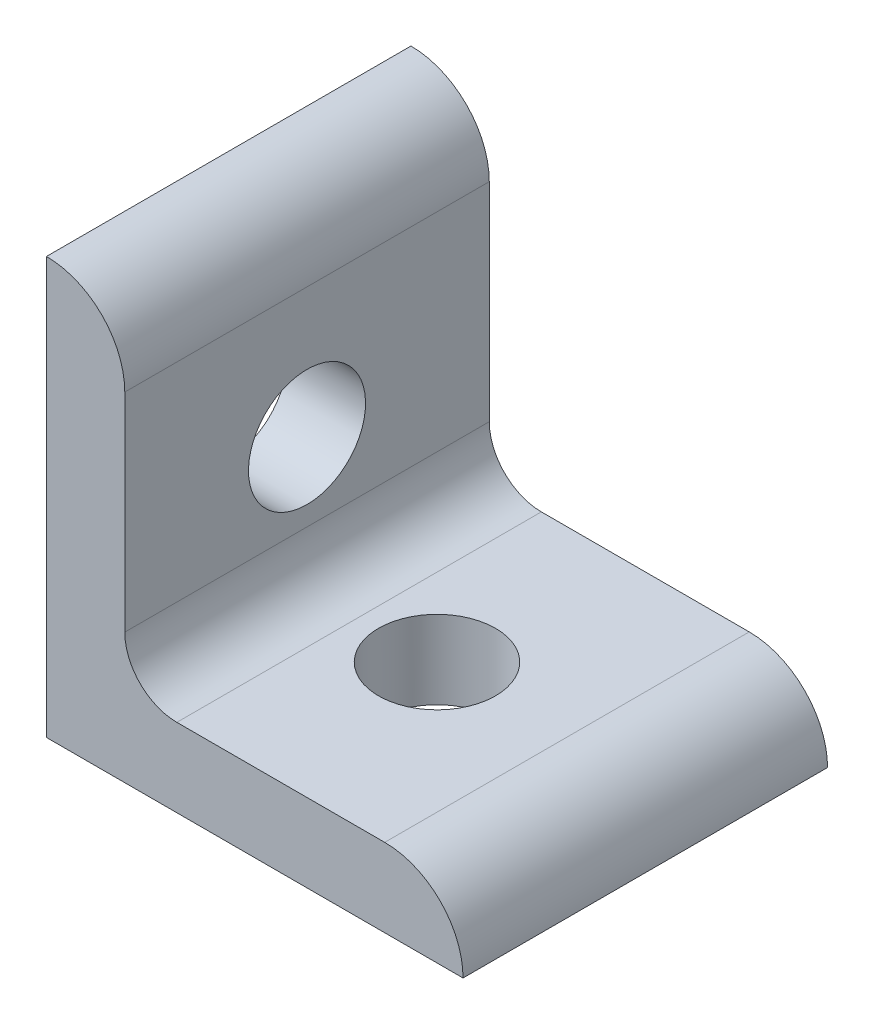
SolidWorks part; units mm, degrees
ref_plane "Front Plane" through (0, 0, 0) normal (0, 0, 1) x (1, 0, 0)
ref_plane "Top Plane" through (0, 0, 0) normal (0, 1, 0) x (1, 0, 0)
ref_plane "Right Plane" through (0, 0, 0) normal (1, 0, 0) x (0, 0, -1)
sketch "Sketch1" plane through (0, 0, 0) normal (0, 0, 1) x (1, 0, 0)
  line L0 (0, 0) -> (0, 25.4)
  line L1 (4.7752, 20.6248) -> (4.7752, 25.4) construction
  line L2 (4.7752, 20.6248) -> (4.7752, 7.9502)
  line L3 (7.9502, 4.7752) -> (20.6248, 4.7752)
  line L4 (4.7752, 25.4) -> (0, 25.4) construction
  line L5 (25.4, 0) -> (0, 0)
  line L6 (20.6248, 4.7752) -> (25.4, 4.7752) construction
  line L7 (25.4, 4.7752) -> (25.4, 0) construction
  arc A0 (4.7752, 20.6248) -> (0, 25.4) centre (0, 20.6248) ccw
  arc A1 (25.4, 0) -> (20.6248, 4.7752) centre (20.6248, 0) ccw
  arc A2 (4.7752, 7.9502) -> (7.9502, 4.7752) centre (7.9502, 7.9502) ccw
  point P10 (4.7752, 23.0124)
  dimension "E" = 3.175
  dimension "D" = 4.7752
  dimension "C" = 25.4
  dimension "B" = 25.4
extrude "Boss-Extrude1" add sketch "Sketch1" along normal mid plane 22.225
sketch "Sketch2" plane through (0, 0, 0) normal (0, 1, 0) x (1, 0, 0)
  line L0 (0, 0) -> (12.7, 0) construction
  circle A0 centre (12.7, 0) radius 3.5687
  dimension "D1" = 12.7
  dimension "E" = 7.1374
extrude "Cut-Extrude1" cut sketch "Sketch2" along normal through all
sketch "Sketch3" plane through (0, 0, 0) normal (1, 0, 0) x (0, 0, -1)
  line L0 (0, 0) -> (0, 12.7) construction
  circle A0 centre (0, 12.7) radius 3.5687
  dimension "D1" = 12.7
  dimension "E" = 7.1374
extrude "Cut-Extrude2" cut sketch "Sketch3" along normal through all
equation "\"E@Sketch3\" = \"E@Sketch2\""
equation "\"D1@Sketch3\" = \"D1@Sketch2\""
